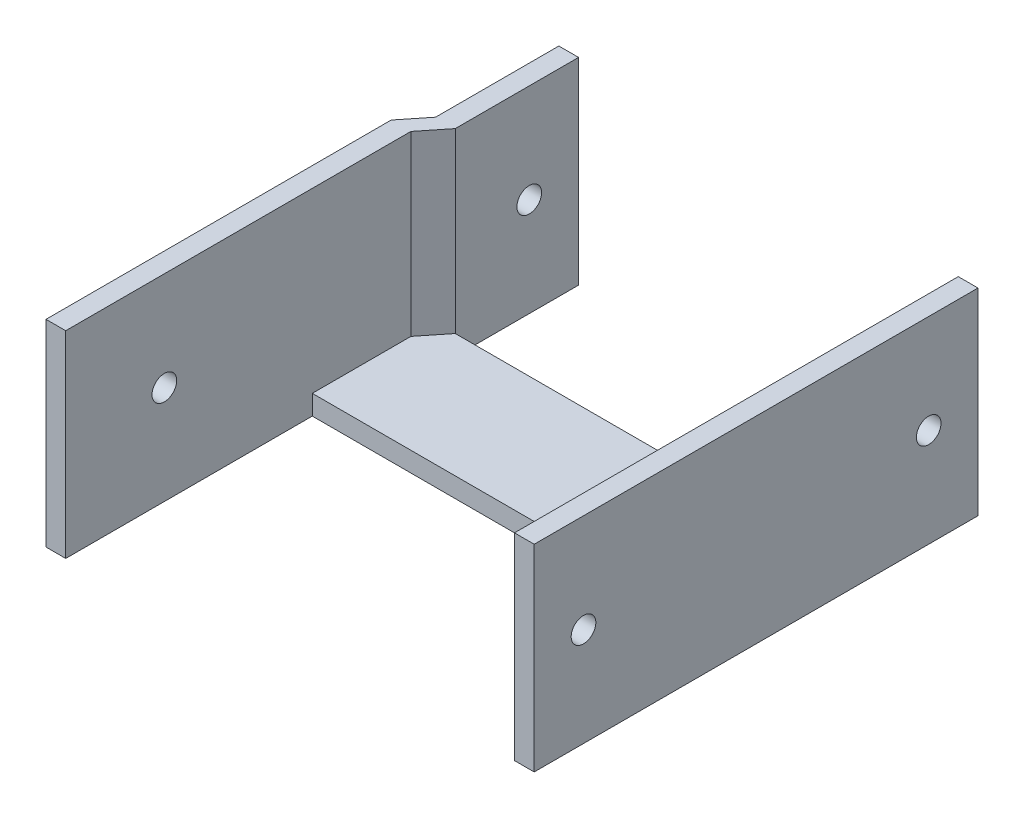
SolidWorks part; units mm, degrees
ref_plane "Alzado" through (0, 0, 0) normal (0, 0, 1) x (1, 0, 0)
ref_plane "Planta" through (0, 0, 0) normal (0, 1, 0) x (1, 0, 0)
ref_plane "Vista lateral" through (0, 0, 0) normal (1, 0, 0) x (0, 0, -1)
sketch "Croquis2" plane through (0, 0, 0) normal (0, 0, 1) x (1, 0, 0)
  line L0 (-41.9814, 0) -> (47.0186, 0)
  line L1 (47.0186, 0) -> (47.0186, 40)
  line L2 (-41.9814, 0) -> (-41.9814, 40)
  line L3 (47.0186, 40) -> (43.0186, 40)
  line L4 (-41.9814, 40) -> (-37.9814, 40)
  line L5 (-37.9814, 4) -> (43.0186, 4)
  line L6 (-37.9814, 40) -> (-37.9814, 4)
  line L7 (43.0186, 40) -> (43.0186, 4)
  line L9 (-37.9814, 40) -> (-33.9814, 40)
  line L10 (-37.9814, 40) -> (-37.9814, 10)
  line L11 (-37.9814, 10) -> (-33.9814, 10)
  line L12 (-33.9814, 40) -> (-33.9814, 10)
  dimension "D1" = 40
  dimension "D2" = 40
  dimension "D3" = 89
  dimension "D4" = 4
  dimension "D5" = 4
  dimension "D6" = 4
  dimension "D7" = 30
  dimension "D8" = 4
extrude "Saliente-Extruir1" add sketch "Croquis2" along normal blind 105 contours L3 L7 L5 L6 L4 L2 L0 L1
sketch "Croquis3" plane through (0, 0, 0) normal (0, 0, 1) x (1, 0, 0)
  line L1 (-37.9814, 40) -> (-33.9814, 40)
  line L2 (-37.9814, 40) -> (-37.9814, 10)
  line L3 (-37.9814, 10) -> (-33.9814, 10)
  line L4 (-33.9814, 40) -> (-33.9814, 10)
  dimension "D1" = 30
  dimension "D2" = 4
extrude "Saliente-Extruir2" add sketch "Croquis3" along normal blind 30
sketch "Croquis4" plane through (0, 4, 0) normal (0, 1, 0) x (1, 0, 0)
  line L0 (43.0186, -105) -> (43.0186, 0) construction
  line L1 (-33.9814, 0) -> (43.0186, 0)
  line L2 (-33.9814, 0) -> (-33.9814, -30)
  line L3 (-33.9814, -30) -> (43.0186, -30)
  line L4 (43.0186, 0) -> (43.0186, -30)
  dimension "D1" = 30
extrude "Cortar-Extruir1" cut sketch "Croquis4" against normal blind 30
sketch "Croquis5" plane through (0, 4, 0) normal (0, 1, 0) x (1, 0, 0)
  line L1 (-37.9814, -105) -> (43.0186, -105)
  line L2 (-37.9814, -105) -> (-37.9814, -55)
  line L3 (-37.9814, -55) -> (43.0186, -55)
  line L4 (43.0186, -105) -> (43.0186, -55)
  line L7 (-33.9814, -30) -> (43.0186, -30) construction
  dimension "D1" = 25
extrude "Cortar-Extruir2" cut sketch "Croquis5" against normal blind 30
sketch "Croquis6" plane through (0, 40, 0) normal (0, 1, 0) x (1, 0, 0)
  line L0 (-24.1118, -30) -> (-78.5535, -30) construction
  line L1 (-33.9814, -30) -> (43.0186, -30) construction
  line L2 (-24.1118, -35) -> (-78.5535, -35) construction
  line L3 (-33.9814, -30) -> (-37.9814, -35)
  line L4 (-37.9814, -105) -> (-37.9814, -30) construction
  line L5 (-41.9814, -35) -> (-37.9814, -30)
  line L6 (-41.9814, -105) -> (-41.9814, 0) construction
  line L7 (-41.9814, -30) -> (-41.9814, -35)
  line L8 (-41.9814, 0) -> (-37.9814, 0)
  line L9 (-41.9814, 0) -> (-41.9814, -30)
  line L10 (-41.9814, -30) -> (-37.9814, -30)
  line L11 (-37.9814, 0) -> (-37.9814, -30)
  line M3 (-33.9814, 0) -> (-41.9814, 0)
  line M4 (-41.9814, 0) -> (-41.9814, -105)
  dimension "D1" = 5
extrude "Cortar-Extruir3" cut sketch "Croquis6" against normal blind 70 contours L11 L10 M3 M4 | L10 L5 M4
sketch "Croquis7" plane through (-37.9814, 0, 0) normal (-1, 0, 0) x (0, 0, 1)
  line L1 (0, 10) -> (30, 10)
  line L2 (0, 10) -> (0, 4)
  line L3 (0, 4) -> (30, 4)
  line L4 (30, 10) -> (30, 4)
sketch "Croquis8" plane through (0, 40, 0) normal (0, 1, 0) x (1, 0, 0)
  line L0 (-37.9814, -30) -> (-33.9814, -30)
  line L1 (-33.9814, -30) -> (-37.9814, -35)
  line L2 (-37.9814, -55) -> (-37.9814, -30) construction
  line L3 (-37.9814, -35) -> (-37.9814, -30)
extrude "Saliente-Extruir4" add sketch "Croquis8" against normal blind 40
extrude "Saliente-Extruir5" add sketch "Croquis7" against normal blind 4
sketch "Croquis10" plane through (47.0186, 0, 0) normal (1, 0, 0) x (0, 0, -1)
  line L0 (-105, 0) -> (0, 0) construction
  line L1 (0, 40) -> (-5, 40)
  line L2 (0, 40) -> (0, 0)
  line L3 (0, 0) -> (-5, 0)
  line L4 (-5, 40) -> (-5, 0)
  dimension "D1" = 5
extrude "Cortar-Extruir5" cut sketch "Croquis10" against normal blind 4
sketch "Croquis11" plane through (47.0186, 0, 0) normal (1, 0, 0) x (0, 0, -1)
  line L0 (-105, 40) -> (-5, 40) construction
  line L1 (-5, 0) -> (-95, 0)
  line L2 (-5, 0) -> (-5, 40)
  line L3 (-5, 40) -> (-95, 40)
  line L4 (-95, 0) -> (-95, 40)
  line L6 (-105, 40) -> (-95, 40)
  line L7 (-105, 40) -> (-105, 0)
  line L8 (-105, 0) -> (-95, 0)
  line L9 (-95, 40) -> (-95, 0)
  line M2 (-105, 0) -> (-5, 0)
  line M4 (-5, 40) -> (-105, 40)
  line M5 (-105, 40) -> (-105, 0)
  dimension "D1" = 90
extrude "Cortar-Extruir6" cut sketch "Croquis11" against normal blind 4 contours L4 M2 M4 M5
sketch "Croquis12" plane through (47.0186, 0, 0) normal (1, 0, 0) x (0, 0, -1)
  line L0 (-5, 40) -> (-5, 0) construction
  line L1 (-95, 40) -> (-5, 40) construction
  line L2 (-95, 0) -> (-95, 40) construction
  circle A0 centre (-15, 20) radius 2.5
  circle A1 centre (-85, 20) radius 2.5
  dimension "D1" = 10
  dimension "D2" = 20
  dimension "D3" = 10
  dimension "D4" = 20
extrude "Cortar-Extruir7" cut sketch "Croquis12" against normal through all
sketch "Croquis13" plane through (-37.9814, 0, 0) normal (-1, 0, 0) x (0, 0, 1)
  line L1 (0, 40) -> (5, 40)
  line L2 (0, 40) -> (0, 0)
  line L3 (0, 0) -> (5, 0)
  line L4 (5, 40) -> (5, 0)
extrude "Cortar-Extruir8" cut sketch "Croquis13" against normal blind 10
